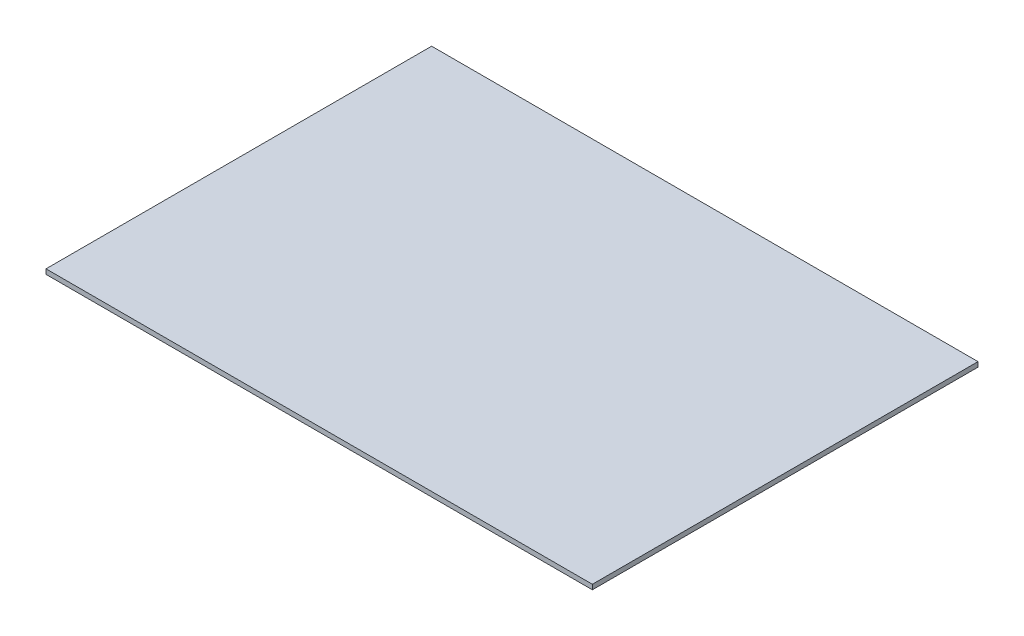
SolidWorks part; units mm, degrees
ref_plane "Front Plane" through (0, 0, 0) normal (0, 0, 1) x (1, 0, 0)
ref_plane "Top Plane" through (0, 0, 0) normal (0, 1, 0) x (1, 0, 0)
ref_plane "Right Plane" through (0, 0, 0) normal (1, 0, 0) x (0, 0, -1)
sketch "Sketch1" plane through (0, 0, 0) normal (0, 1, 0) x (1, 0, 0)
  line L1 (-115.9583, -86.2755) -> (171.5254, -86.2755)
  line L2 (-115.9583, -86.2755) -> (-115.9583, 116.6284)
  line L3 (-115.9583, 116.6284) -> (171.5254, 116.6284)
  line L4 (171.5254, -86.2755) -> (171.5254, 116.6284)
extrude "Extrude1" add sketch "Sketch1" along normal blind 2.54
